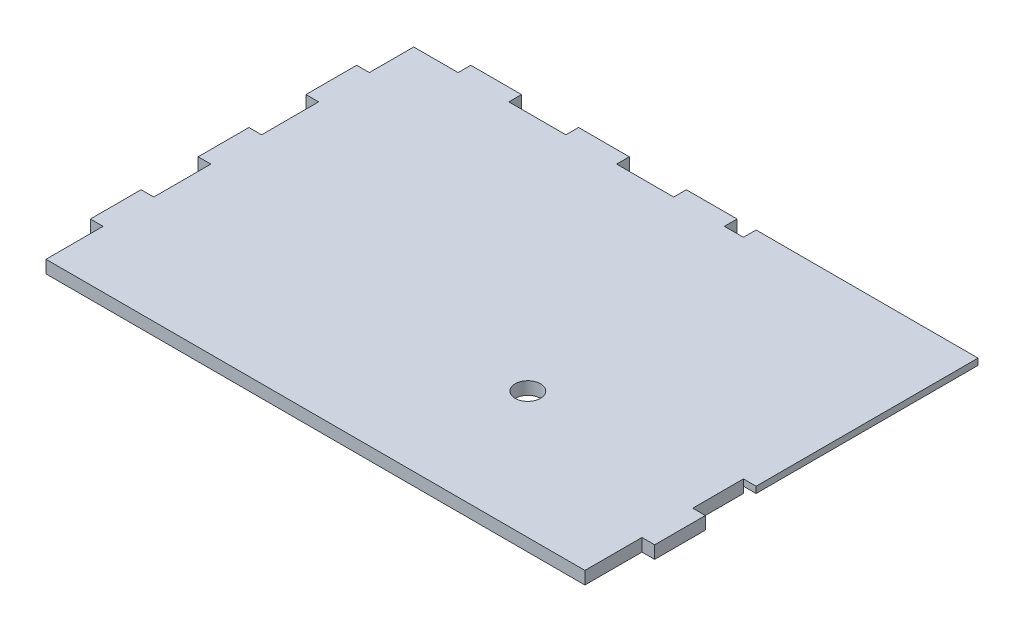
SolidWorks part; units mm, degrees
ref_plane "前视基准面" through (0, 0, 0) normal (0, 0, 1) x (1, 0, 0)
ref_plane "上视基准面" through (0, 0, 0) normal (0, 1, 0) x (1, 0, 0)
ref_plane "右视基准面" through (0, 0, 0) normal (1, 0, 0) x (0, 0, -1)
sketch "顶盖基体图" plane through (0, 0, 0) normal (0, 1, 0) x (1, 0, 0)
  line L1 (-44.5, 30) -> (44.5, 30)
  line L2 (-44.5, 30) -> (-44.5, -30)
  line L3 (-44.5, -30) -> (44.5, -30)
  line L4 (44.5, 30) -> (44.5, -30)
  line L5 (-44.5, 30) -> (44.5, -30) construction
  line L6 (-44.5, -30) -> (44.5, 30) construction
  point P0 (0, 0)
  dimension "D1" = 60
  dimension "D2" = 89
extrude "顶盖基体" add sketch "顶盖基体图" along normal blind 2
sketch "外边缘切除图" plane through (0, 2, 0) normal (0, 1, 0) x (1, 0, 0)
  line L0 (-44.5, -30) -> (-42.5, -30)
  line L1 (-44.5, 30) -> (-44.5, -30) construction
  line L2 (-44.5, -30) -> (44.5, -30) construction
  line L3 (-42.5, -30) -> (-42.5, 28)
  line L4 (-42.5, 28) -> (9.5, 28)
  line L5 (9.5, 28) -> (9.5, 30)
  line L6 (44.5, 30) -> (-44.5, 30) construction
  line L7 (9.5, 30) -> (-44.5, 30)
  line L8 (-44.5, 30) -> (-44.5, -30)
  line L9 (44.5, -30) -> (44.5, 30) construction
  dimension "D1" = 2
  dimension "D2" = 2
  dimension "D3" = 35
extrude "外边缘切除" cut sketch "外边缘切除图" against normal blind 2
sketch "内边缘切除图" plane through (0, 2, 0) normal (0, 1, 0) x (1, 0, 0)
  line L0 (44.5, 30) -> (9.5, 30) construction
  line L1 (44.5, -30) -> (42.5, -30)
  line L2 (44.5, -30) -> (44.5, -5)
  line L3 (44.5, -5) -> (42.5, -5)
  line L4 (42.5, -30) -> (42.5, -5)
  dimension "D1" = 2
  dimension "D2" = 35
extrude "内边缘切除" cut sketch "内边缘切除图" against normal blind 2
sketch "外边缘卡槽图" plane through (-42.5, 0, 0) normal (-1, 0, 0) x (0, 0, 1)
  line L0 (30, 2) -> (-28, 2) construction
  line L1 (21, 2) -> (13, 2)
  line L2 (21, 2) -> (21, 0)
  line L3 (21, 0) -> (13, 0)
  line L4 (13, 2) -> (13, 0)
  line L5 (30, 0) -> (-28, 0) construction
  line L6 (30, 0) -> (30, 2) construction
  line L7 (4, 2) -> (-4, 2)
  line L8 (4, 2) -> (4, 0)
  line L9 (4, 0) -> (-4, 0)
  line L10 (-4, 2) -> (-4, 0)
  line L11 (-13, 2) -> (-21, 2)
  line L12 (-13, 2) -> (-13, 0)
  line L13 (-13, 0) -> (-21, 0)
  line L14 (-21, 2) -> (-21, 0)
  line L15 (21, 2) -> (4, 2) construction
  point P10 (30, 1)
  dimension "D1" = 8
  dimension "D2" = 9
  dimension "D4" = 17
  dimension "D3" = 3
extrude "外边缘卡槽" add sketch "外边缘卡槽图" along normal blind 2
sketch "后边缘卡槽图" plane through (0, 0, -28) normal (0, 0, -1) x (-1, 0, 0)
  line L0 (42.5, 2) -> (-9.5, 2) construction
  line L1 (27.5, 2) -> (35.5, 2)
  line L2 (27.5, 2) -> (27.5, 0)
  line L3 (27.5, 0) -> (35.5, 0)
  line L4 (35.5, 2) -> (35.5, 0)
  line L5 (42.5, 0) -> (-9.5, 0) construction
  line L6 (42.5, 0) -> (42.5, 2) construction
  line L7 (10.5, 2) -> (18.5, 2)
  line L8 (10.5, 2) -> (10.5, 0)
  line L9 (10.5, 0) -> (18.5, 0)
  line L10 (18.5, 2) -> (18.5, 0)
  line L11 (-6.5, 2) -> (1.5, 2)
  line L12 (-6.5, 2) -> (-6.5, 0)
  line L13 (-6.5, 0) -> (1.5, 0)
  line L14 (1.5, 2) -> (1.5, 0)
  line L15 (27.5, 2) -> (10.5, 2) construction
  point P10 (42.5, 1)
  dimension "D1" = 8
  dimension "D2" = 7
  dimension "D4" = 17
  dimension "D3" = 3
extrude "后边缘卡槽" add sketch "后边缘卡槽图" along normal blind 2
sketch "内边缘卡槽图" plane through (42.5, 0, 0) normal (1, 0, 0) x (0, 0, -1)
  line L0 (-5, 2) -> (-30, 2) construction
  line L1 (-21, 2) -> (-13, 2)
  line L2 (-21, 2) -> (-21, 0)
  line L3 (-21, 0) -> (-13, 0)
  line L4 (-13, 2) -> (-13, 0)
  line L5 (-5, 0) -> (-30, 0) construction
  line L6 (-30, 0) -> (-30, 2) construction
  point P10 (-30, 1)
  dimension "D1" = 8
  dimension "D2" = 9
extrude "内边缘卡槽" add sketch "内边缘卡槽图" along normal blind 2
sketch "连接件对其图" plane through (0, 0, 0) normal (0, -1, 0) x (1, 0, 0)
  line L0 (44.5, -30) -> (9.5, -30)
  line L1 (44.5, -30) -> (9.5, -30) construction
  line L2 (9.5, -30) -> (9.5, -23)
  line L3 (9.5, -23) -> (37.5, 5)
  line L4 (37.5, 5) -> (44.5, 5)
  line L5 (44.5, 5) -> (44.5, -30) construction
  line L6 (44.5, 5) -> (44.5, -30)
  dimension "D1" = 35
  dimension "D2" = 35
  dimension "D3" = 7
  dimension "D4" = 7
extrude "连接件对齐" cut sketch "连接件对其图" against normal blind 1
sketch "螺丝扣图" plane through (0, 2, 0) normal (0, 1, 0) x (1, 0, 0)
  line L0 (-44.5, -21) -> (-44.5, -13) construction
  line L1 (-42.5, -30) -> (42.5, -30) construction
  circle A0 centre (13.5, -10) radius 2
  point P4 (-44.5, -17)
  dimension "D1" = 4
  dimension "D2" = 58
  dimension "D3" = 20
extrude "螺丝扣" cut sketch "螺丝扣图" against normal through all
